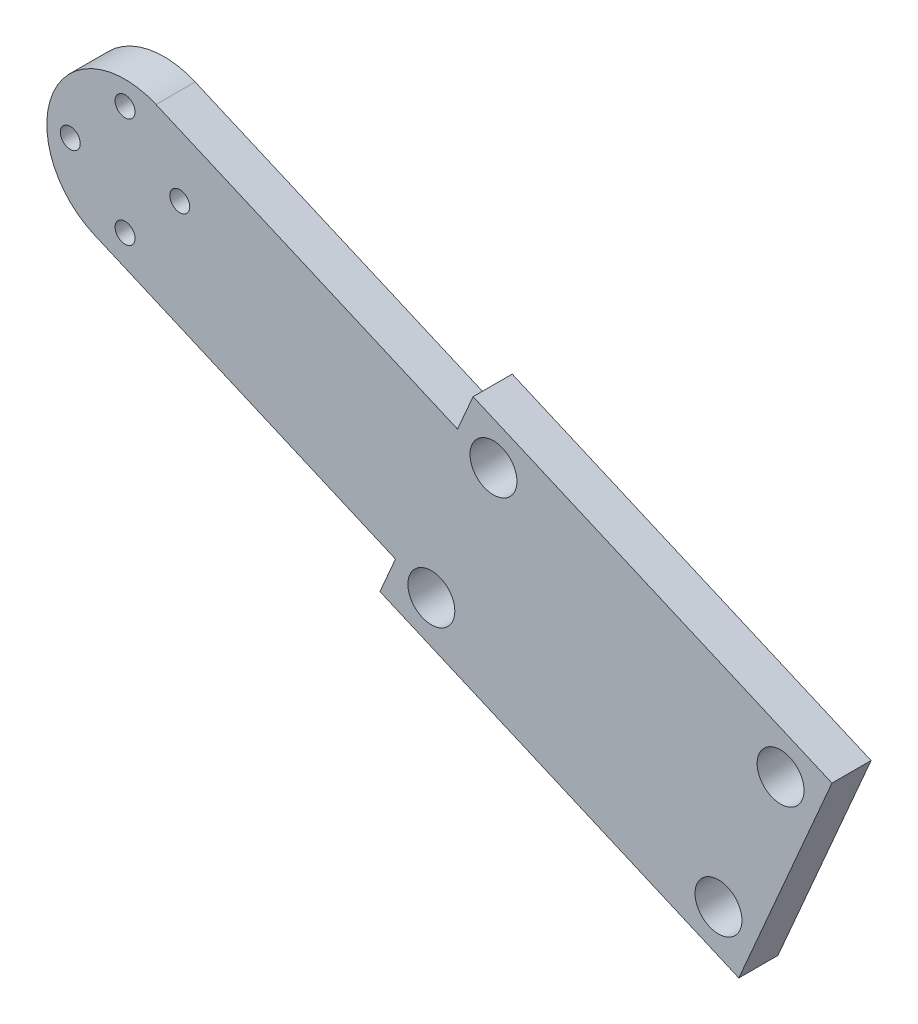
SolidWorks part; units mm, degrees
ref_plane "Plan de face" through (0, 0, 0) normal (0, 0, 1) x (1, 0, 0)
ref_plane "Plan de dessus" through (0, 0, 0) normal (0, 1, 0) x (1, 0, 0)
ref_plane "Plan de droite" through (0, 0, 0) normal (1, 0, 0) x (0, 0, -1)
sketch "Esquisse2" plane through (0, 0, 0) normal (0, 0, 1) x (1, 0, 0)
  line L1 (42.5187, -7.494) -> (3.9696, 9.1784)
  line L2 (34.5795, -25.8507) -> (-3.9696, -9.1784)
  line L7 (32.5947, -30.4399) -> (34.5795, -25.8507)
  line L8 (32.5947, -30.4399) -> (78.4865, -50.2879)
  line L9 (44.5035, -2.9048) -> (90.3953, -22.7528)
  line L10 (78.4865, -50.2879) -> (90.3953, -22.7528)
  line L14 (42.5187, -7.494) -> (44.5035, -2.9048)
  arc A0 (3.9696, 9.1784) -> (-3.9696, -9.1784) centre (0, 0) ccw
  circle A2 centre (7, 0) radius 1.275
  circle A5 centre (0, 7) radius 1.275
  circle A7 centre (-7, 0) radius 1.275
  circle A9 centre (0, -7) radius 1.275
  circle A11 centre (75.8821, -43.7139) radius 3
  circle A13 centre (83.8213, -25.3572) radius 3
  circle A15 centre (47.1079, -9.4788) radius 3
  circle A17 centre (39.1687, -27.8355) radius 3
  dimension "D1" = 2.55
  dimension "D2" = 6
  dimension "D3" = 10
  dimension "D4" = 3.9696
  dimension "D5" = 7
  dimension "D6" = 5
  dimension "D8" = 5
  dimension "D7" = 5
  dimension "D9" = 5
  dimension "D10" = 5
  dimension "D11" = 40
  dimension "D12" = 92
  dimension "D13" = 7
  dimension "D14" = 7
  dimension "D15" = 7
extrude "Boss.-Extru.1" add sketch "Esquisse2" along normal blind 5
